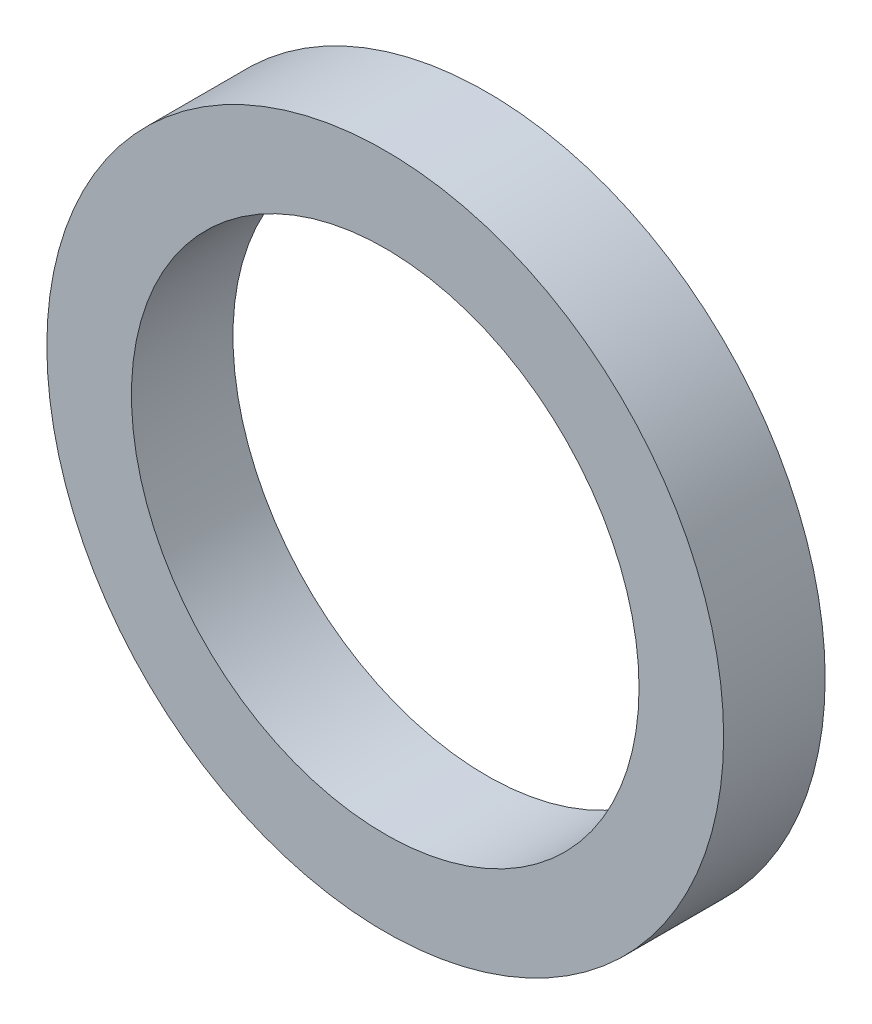
SolidWorks part; units mm, degrees
material "Nylon 101"
ref_plane "Front" through (0, 0, 0) normal (0, 0, 1) x (1, 0, 0)
ref_plane "Top" through (0, 0, 0) normal (0, 1, 0) x (1, 0, 0)
ref_plane "Right" through (0, 0, 0) normal (1, 0, 0) x (0, 0, -1)
sketch "Sketch1" plane through (0, 0, 0) normal (0, 0, 1) x (1, 0, 0)
  circle A0 centre (0, 0) radius 4.7625
  circle A1 centre (0, 0) radius 6.35
  dimension "D1" = 12.7
  dimension "D2" = 9.525
extrude "Boss-Extrude1" add sketch "Sketch1" along normal blind 1.905
